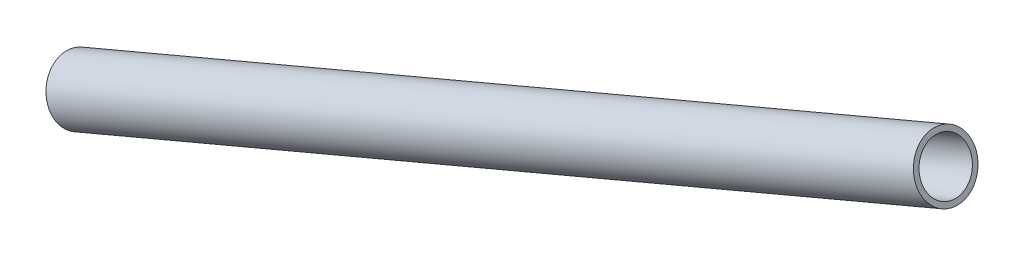
SolidWorks part; units mm, degrees
ref_plane "Front" through (0, 0, 0) normal (0, 0, 1) x (1, 0, 0)
ref_plane "Top" through (0, 0, 0) normal (0, 1, 0) x (1, 0, 0)
ref_plane "Right" through (0, 0, 0) normal (1, 0, 0) x (0, 0, -1)
sketch "Sketch1" plane through (0, 0, 0) normal (0, 0, 1) x (1, 0, 0)
  line L0 (-232.7546, -1448.8276) -> (-232.1113, -1450.3481)
  line L1 (-232.1113, -1450.3481) -> (-506.6174, -1566.4911)
  line L2 (-506.6174, -1566.4911) -> (-507.2607, -1564.9706)
  line L3 (-507.2607, -1564.9706) -> (-232.7546, -1448.8276)
  line L4 (-235.8228, -1441.576) -> (-510.3289, -1557.719) construction
  line L5 (-571.5, -1583.6003) -> (-190.5, -1422.4) construction
  line L6 (-510.3289, -1557.719) -> (-507.2607, -1564.9706) construction
  line L7 (-232.7546, -1448.8276) -> (-235.8228, -1441.576) construction
  dimension "D1" = 1.651
  dimension "D2" = 9.525
revolve "Revolve1" add sketch "Sketch1" angle 360 about L4
equation "\"D1@Sketch1\"=\"a arm tube thickness@FS2-SU-FS-A-0002-V1, FRONT LEFT SUSPENSION.SLDASM\""
equation "\"D2@Sketch1\"=\"a arm tube diameter@FS2-SU-FS-A-0002-V1, FRONT LEFT SUSPENSION.SLDASM\"/2"
